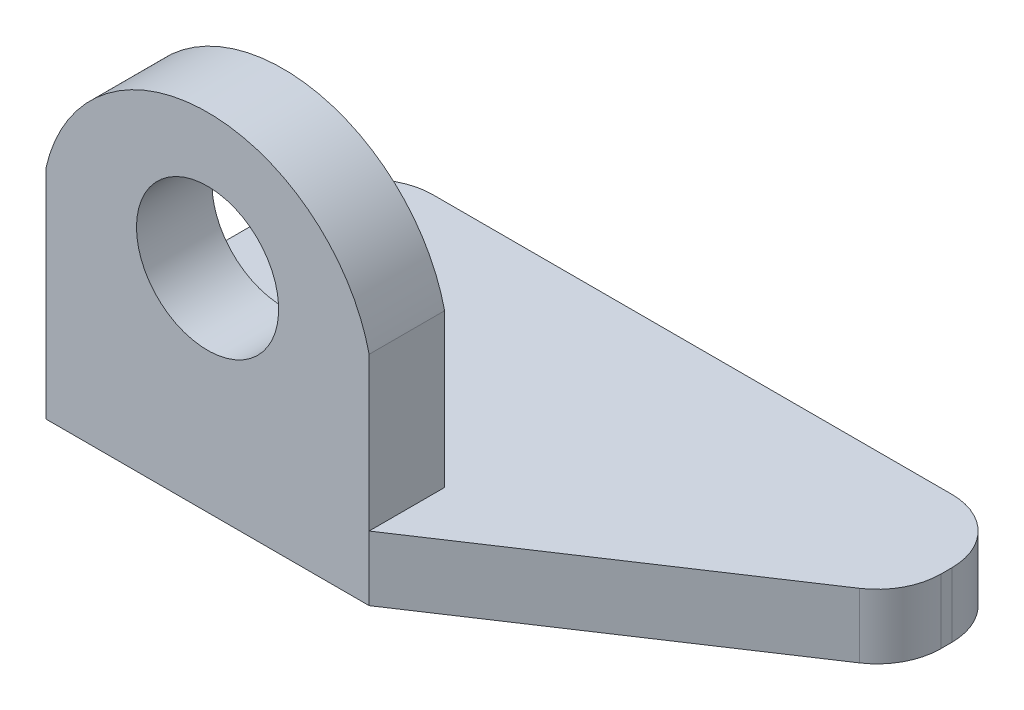
SolidWorks part; units mm, degrees
ref_plane "Front Plane" through (0, 0, 0) normal (0, 0, 1) x (1, 0, 0)
ref_plane "Top Plane" through (0, 0, 0) normal (0, 1, 0) x (1, 0, 0)
ref_plane "Right Plane" through (0, 0, 0) normal (1, 0, 0) x (0, 0, -1)
sketch "Sketch1" plane through (0, 0, 0) normal (0, 1, 0) x (1, 0, 0)
  line L0 (-63.4459, 38.9371) -> (38.1541, 38.9371)
  line L1 (38.1541, 38.9371) -> (38.1541, -11.8629)
  line L2 (38.1541, -11.8629) -> (-63.4459, -11.8629)
  line L3 (-63.4459, -11.8629) -> (-63.4459, 38.9371)
  line L4 (-12.6459, -11.8629) -> (38.1541, 21.8412)
  dimension "D1" = 101.6
  dimension "D2" = 101.6
  dimension "D3" = 50.8
  dimension "D4" = 50.8
  dimension "D5" = 50.8
extrude "Boss-Extrude1" add sketch "Sketch1" along normal blind 10.16 contours L2 L4 L1 L0 L3
sketch "Sketch3" plane through (0, 0, 0) normal (0, 0, 1) x (1, 0, 0)
  line L1 (-63.4459, 10.16) -> (-12.6459, 10.16)
  line L2 (-63.4459, 10.16) -> (-63.4459, 34.2245)
  line L3 (-63.4459, 34.2245) -> (-12.6459, 34.2245)
  line L4 (-12.6459, 10.16) -> (-12.6459, 34.2245)
  arc A0 (-63.4459, 34.2245) -> (-12.6459, 34.2245) centre (-38.0459, 28.4198) cw
extrude "Boss-Extrude2" add sketch "Sketch3" along normal up to surface (11.8629 mm away) contours A0 L3 | L1 L4 L3 L2 up to face at (-38.0459, 5.08, 11.8629)
sketch "Sketch4" plane through (0, 0, 0) normal (0, 0, -1) x (-1, 0, 0)
  line L0 (63.4459, 10.16) -> (63.4459, 34.2245) construction
  circle A0 centre (38.0459, 33.2379) radius 11.177
  dimension "D1" = 25.4
extrude "Cut-Extrude2" cut sketch "Sketch4" against normal through all contours A0
fillet "Fillet1" radius 10 1 edges at (38.1541, 5.08, -38.9371)
fillet "Fillet2" radius 10 1 edges at (38.1541, 5.08, -21.8412)
fillet "Fillet3" radius 10 1 edges at (-63.4459, 5.08, -38.9371)
